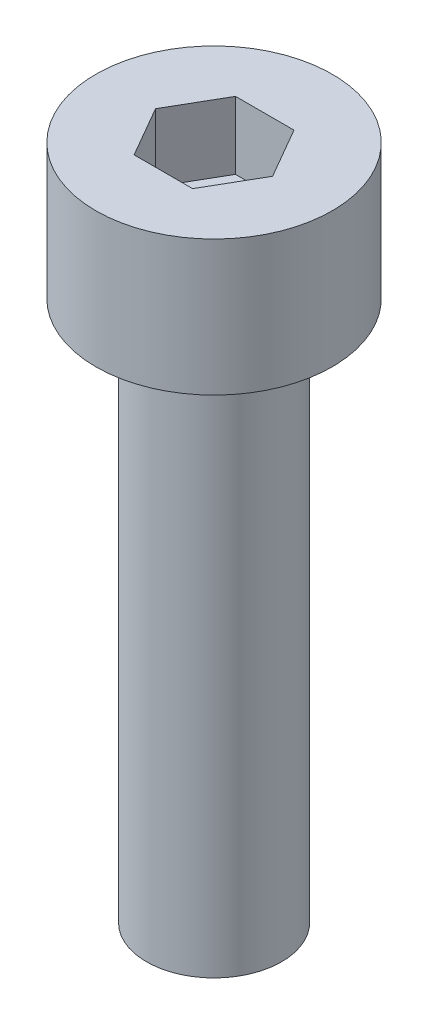
SolidWorks part; units mm, degrees
material "AISI 304"
ref_plane "前视基准面" through (0, 0, 0) normal (0, 0, 1) x (1, 0, 0)
ref_plane "上视基准面" through (0, 0, 0) normal (0, 1, 0) x (1, 0, 0)
ref_plane "右视基准面" through (0, 0, 0) normal (1, 0, 0) x (0, 0, -1)
sketch "草图1" plane through (0, 0, 0) normal (0, 1, 0) x (1, 0, 0)
  circle A0 centre (0, 0) radius 3.5
  dimension "D1" = 7
extrude "杯头" add sketch "草图1" along normal blind 4
sketch "草图2" plane through (0, 4, 0) normal (0, 1, 0) x (1, 0, 0)
  line L1 (1.7321, 0) -> (0.866, 1.5)
  line L2 (0.866, 1.5) -> (-0.866, 1.5)
  line L3 (-0.866, 1.5) -> (-1.7321, 0)
  line L4 (-1.7321, 0) -> (-0.866, -1.5)
  line L5 (-0.866, -1.5) -> (0.866, -1.5)
  line L6 (0.866, -1.5) -> (1.7321, 0)
  circle A0 centre (0, 0) radius 1.5 construction
  dimension "D1" = 3
extrude "内六角口" cut sketch "草图2" against normal blind 2
sketch "草图3" plane through (0, 0, 0) normal (0, -1, 0) x (1, 0, 0)
  circle A0 centre (0, 0) radius 2
  dimension "D1" = 4
extrude "螺纹长度" add sketch "草图3" along normal blind 16
sketch "草图8" [suppressed] plane through (0, 0, 0) normal (0, 0, 1) x (1, 0, 0)
  line L0 (-1.3, -14) -> (-2, -13.3)
  line L1 (-2, -14) -> (2, -14) construction
  line L2 (-2, 0) -> (-2, -14) construction
  line L3 (-2, -13.3) -> (-2, -14)
  line L4 (-2, -14) -> (-1.3, -14)
  dimension "D1" = 0.7
  dimension "D2" = 0.7
